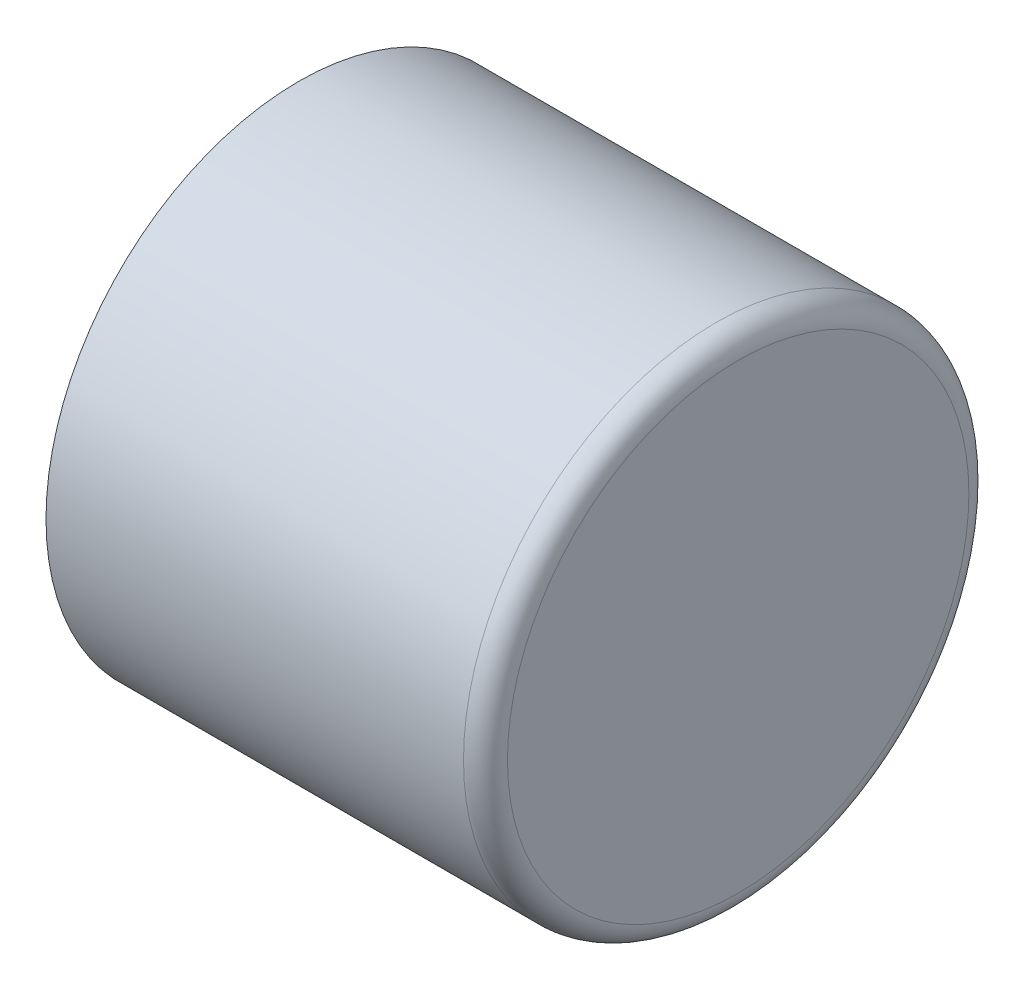
SolidWorks part; units mm, degrees
ref_plane "Front Plane" through (0, 0, 0) normal (0, 0, 1) x (1, 0, 0)
ref_plane "Top Plane" through (0, 0, 0) normal (0, 1, 0) x (1, 0, 0)
ref_plane "Right Plane" through (0, 0, 0) normal (1, 0, 0) x (0, 0, -1)
sketch "Sketch1" plane through (0, 0, 0) normal (1, 0, 0) x (0, 0, -1)
  circle A0 centre (0, 0) radius 12.7
  circle A1 centre (0, 0) radius 14.605
  dimension "D1" = 25.4
  dimension "D2" = 29.21
extrude "Boss-Extrude1" add sketch "Sketch1" along normal blind 25.4
fillet "Fillet1" radius 1.27 1 edges at (25.4, 0, -14.605)
sketch "Sketch3" plane through (25.4, 0, 0) normal (1, 0, 0) x (0, 0, -1)
  circle A0 centre (0, 0) radius 12.7
extrude "Boss-Extrude2" add sketch "Sketch3" against normal blind 1.27
